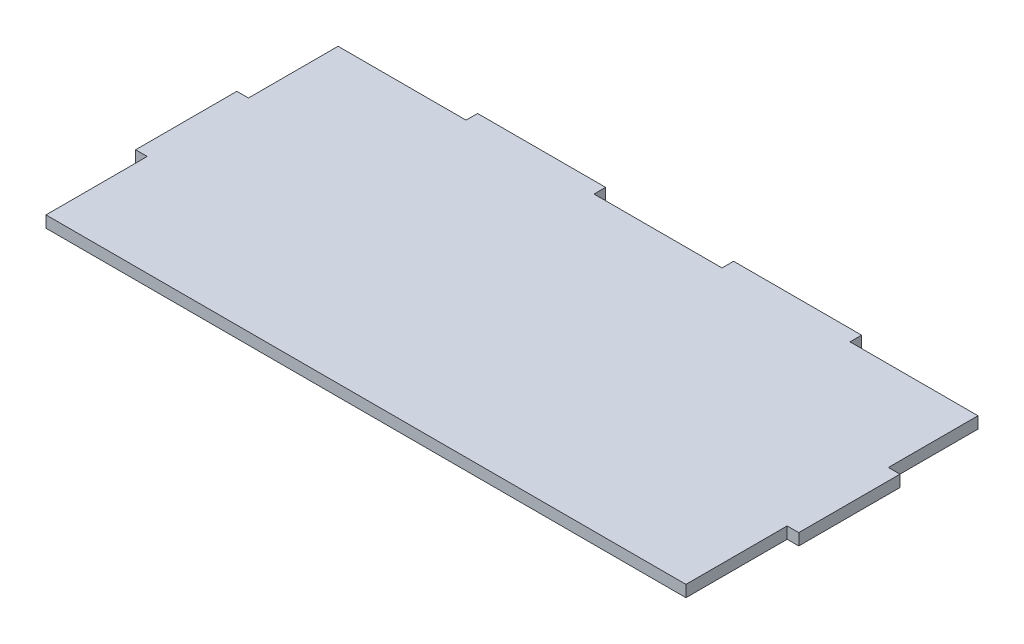
SolidWorks part; units mm, degrees
ref_plane "Front Plane" through (0, 0, 0) normal (0, 0, 1) x (1, 0, 0)
ref_plane "Top Plane" through (0, 0, 0) normal (0, 1, 0) x (1, 0, 0)
ref_plane "Right Plane" through (0, 0, 0) normal (1, 0, 0) x (0, 0, -1)
sketch "Sketch1" plane through (0, 0, 0) normal (0, 1, 0) x (1, 0, 0)
  line L0 (14.3, 49) -> (130.5961, 49) construction
  line L5 (13.3, 21) -> (124.4517, 21) construction
  line L18 (144, 18.5667) -> (144, -5)
  line L21 (74.5, -5) -> (64.5, -5)
  line L27 (-5, 18.5667) -> (-5, -5)
  line L35 (-7.7, 18.5667) -> (-5, 18.5667)
  line L39 (115.82, -5) -> (144, -5)
  line L42 (74.5, -5) -> (84.94, -5)
  line L45 (54.06, -5) -> (64.5, -5)
  line L49 (-5, -5) -> (23.18, -5)
  line L50 (-7.7, 18.5667) -> (-7.7, 42.1333)
  line L51 (-7.7, 42.1333) -> (-5, 42.1333)
  line L56 (-5, 63) -> (-5, 42.1333)
  line L64 (54.06, -5) -> (23.18, -5)
  line L65 (115.82, -5) -> (84.94, -5)
  line L67 (146.7, 18.5667) -> (146.7, 42.1333)
  line L69 (144, 63) -> (144, 42.1333)
  line L72 (146.7, 42.1333) -> (144, 42.1333)
  line L73 (146.7, 18.5667) -> (144, 18.5667)
  line L75 (24.8, 65.7) -> (54.6, 65.7)
  line L77 (84.4, 65.7) -> (114.2, 65.7)
  line L79 (-5, 63) -> (24.8, 63)
  line L80 (24.8, 65.7) -> (24.8, 63)
  line L81 (54.6, 65.7) -> (54.6, 63)
  line L82 (84.4, 65.7) -> (84.4, 63)
  line L83 (114.2, 65.7) -> (114.2, 63)
  line L84 (74.5, 63) -> (84.4, 63)
  line L85 (114.2, 63) -> (144, 63)
  line L86 (54.6, 63) -> (64.5, 63)
  line L87 (74.5, 63) -> (64.5, 63)
extrude "Boss-Extrude1" add sketch "Sketch1" along normal blind 2.7
